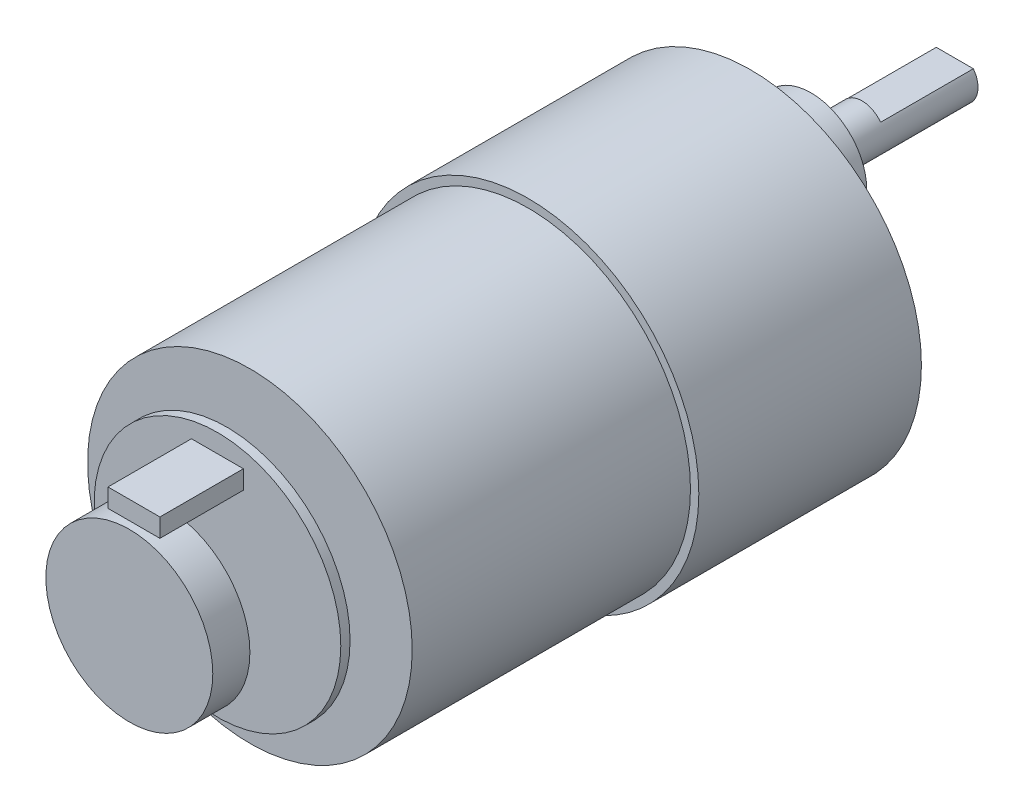
SolidWorks part; units mm, degrees
ref_plane "Plano frontal" through (0, 0, 0) normal (0, 0, 1) x (1, 0, 0)
ref_plane "Plano superior" through (0, 0, 0) normal (0, 1, 0) x (1, 0, 0)
ref_plane "Plano direito" through (0, 0, 0) normal (1, 0, 0) x (0, 0, -1)
sketch "Esboço1" plane through (0, 0, 0) normal (0, 0, 1) x (1, 0, 0)
  circle A0 centre (0, 0) radius 18.4
extrude "Ressalto-extrusão1" add sketch "Esboço1" along normal blind 24
sketch "Esboço2" plane through (0, 0, 24) normal (0, 0, 1) x (1, 0, 0)
  circle A0 centre (0, 0) radius 17.5
extrude "Ressalto-extrusão2" add sketch "Esboço2" along normal blind 30
sketch "Esboço3" plane through (0, 0, 0) normal (0, 0, -1) x (-1, 0, 0)
  line L1 (0, 0) -> (0, 7) construction
  circle A1 centre (0, 7) radius 6
extrude "Ressalto-extrusão3" add sketch "Esboço3" along normal blind 6.5
sketch "Esboço4" plane through (0, 0, -6.5) normal (0, 0, -1) x (-1, 0, 0)
  circle A0 centre (0, 7) radius 2.5
extrude "Ressalto-extrusão4" add sketch "Esboço4" along normal blind 15.5
sketch "Esboço5" plane through (0, 0, 0) normal (0, 0, -1) x (-1, 0, 0)
  line L0 (0, 0) -> (7.4859, 12.966) construction
  circle A0 centre (7.4859, 12.966) radius 1.5
  circle A1 centre (14.9719, 0) radius 1.5
  circle A2 centre (7.4859, -12.966) radius 1.5
  circle A3 centre (-7.4859, -12.966) radius 1.5
  circle A4 centre (-14.9719, 0) radius 1.5
  circle A5 centre (-7.4859, 12.966) radius 1.5
  point P17 (0, 0)
  dimension "D1" = 6
extrude "Corte-extrusão1" cut sketch "Esboço5" against normal blind 10
sketch "Esboço6" plane through (0, 0, 54) normal (0, 0, 1) x (1, 0, 0)
  circle A0 centre (0, 0) radius 1
extrude "Ressalto-extrusão5" add sketch "Esboço6" along normal blind 2.5
sketch "Esboço8" plane through (0, 0, 56.5) normal (0, 0, 1) x (1, 0, 0)
  circle A0 centre (0, 0) radius 13.3
extrude "Ressalto-extrusão7" add sketch "Esboço8" along normal blind 1
sketch "Esboço9" plane through (0, 0, 57.5) normal (0, 0, 1) x (1, 0, 0)
  circle A0 centre (0, 0) radius 1
extrude "Ressalto-extrusão8" add sketch "Esboço9" along normal blind 5.5
sketch "Esboço10" plane through (0, 0, 63) normal (0, 0, 1) x (1, 0, 0)
  circle A0 centre (0, 0) radius 9
extrude "Ressalto-extrusão9" add sketch "Esboço10" along normal blind 4
sketch "Esboço11" plane through (0, 0, 57.5) normal (0, 0, 1) x (1, 0, 0)
  line L0 (0, 13.3) -> (0, 10.3) construction
  line L2 (-2.8, 11.3) -> (2.8, 11.3)
  line L3 (-2.8, 11.3) -> (-2.8, 9.3)
  line L4 (-2.8, 9.3) -> (2.8, 9.3)
  line L5 (2.8, 11.3) -> (2.8, 9.3)
  line L6 (-2.8, 11.3) -> (2.8, 9.3) construction
  line L7 (-2.8, 9.3) -> (2.8, 11.3) construction
  circle A0 centre (0, 0) radius 13.3 construction
extrude "Ressalto-extrusão10" add sketch "Esboço11" along normal blind 9
sketch "Esboço12" plane through (0, 0, -22) normal (0, 0, -1) x (-1, 0, 0)
  line L0 (0, 4.5) -> (0, 8.5) construction
  line L2 (2, 8.5) -> (-2, 8.5)
  circle A0 centre (0, 7) radius 2.5 construction
  arc A1 (-2, 8.5) -> (2, 8.5) centre (0, 7) ccw
extrude "Corte-extrusão2" cut sketch "Esboço12" against normal blind 10 flip side to cut
